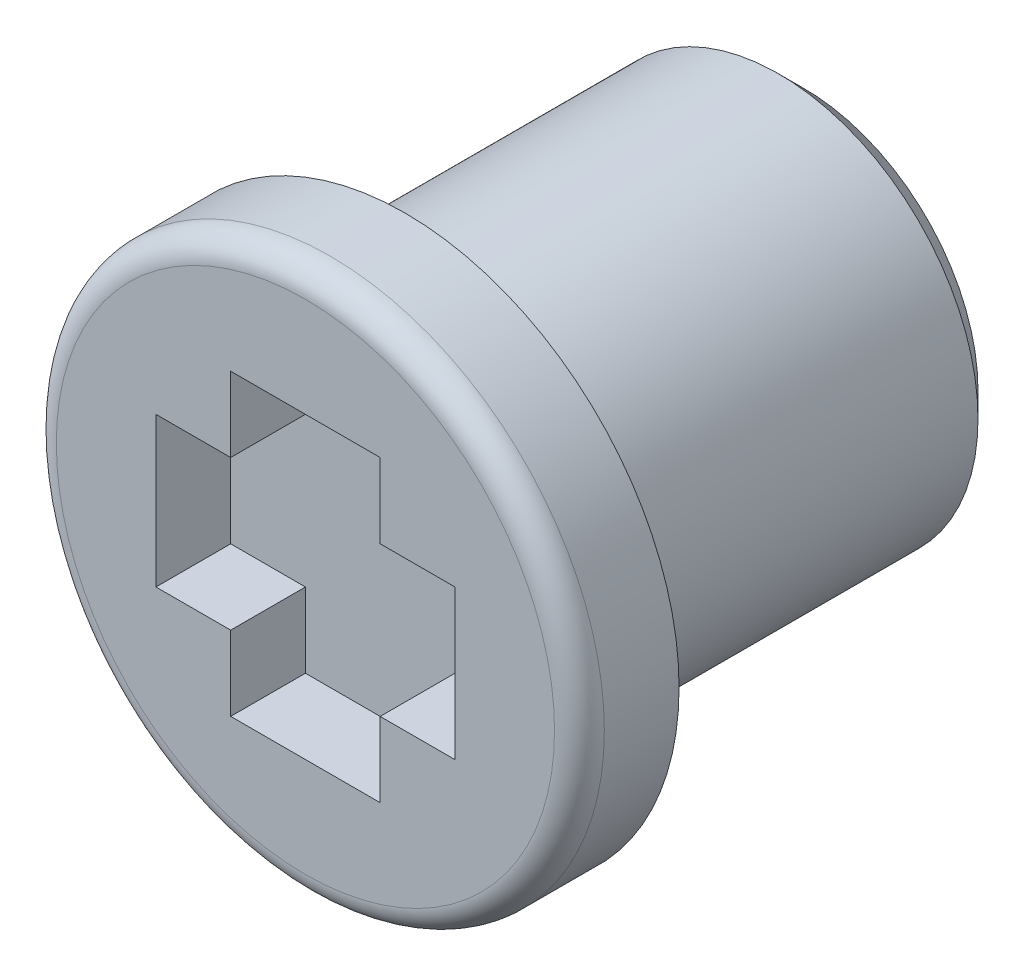
SolidWorks part; units mm, degrees
ref_plane "Front Plane" through (0, 0, 0) normal (0, 0, 1) x (1, 0, 0)
ref_plane "Top Plane" through (0, 0, 0) normal (0, 1, 0) x (1, 0, 0)
ref_plane "Right Plane" through (0, 0, 0) normal (1, 0, 0) x (0, 0, -1)
sketch "Sketch1" plane through (0, 0, 0) normal (0, 0, 1) x (1, 0, 0)
  circle A0 centre (0, 0.1694) radius 4
  dimension "D1" = 8
extrude "Boss-Extrude1" add sketch "Sketch1" along normal blind 8
sketch "Sketch2" plane through (0, 0, 8) normal (0, 0, 1) x (1, 0, 0)
  circle A0 centre (0, 0) radius 5.5
  dimension "D1" = 11
extrude "Boss-Extrude2" add sketch "Sketch2" along normal blind 2
chamfer "Chamfer1" distance 0.5 angle 45 1 edges at (4, 0.1694, 0)
sketch "Sketch4" plane through (0, 0, 10) normal (0, 0, 1) x (1, 0, 0)
  line L0 (-4.6717, 0) -> (-3, 0) construction
  line L2 (1.5, 1.5) -> (3, 1.5)
  line L3 (0, 3) -> (-1.5, 3)
  line L4 (-1.5, 3) -> (-1.5, 1.5)
  line L5 (-3, 0) -> (-3, 1.5)
  line L6 (-3, 1.5) -> (-1.5, 1.5)
  line L7 (0, 3) -> (1.5, 3)
  line L8 (1.5, 3) -> (1.5, 1.5)
  line L9 (-1.5, -3) -> (1.5, -3)
  line L10 (-3, 0) -> (-3, -1.5009)
  line L11 (-3, -1.5009) -> (-1.5, -1.5009)
  line L12 (3, 1.5) -> (3, -1.5009)
  line L13 (3, -1.5009) -> (1.5, -1.5009)
  line L14 (-1.5, -1.5009) -> (-1.5, -3)
  line L15 (1.5, -1.5009) -> (1.5, -3)
  line L16 (3, 0) -> (4.18, 0) construction
  dimension "D3" = 1.5
  dimension "D4" = 6
  dimension "D5" = 1.5
  dimension "D6" = 6
  dimension "D7" = 1.5
  dimension "D8" = 6
extrude "Cut-Extrude1" cut sketch "Sketch4" against normal blind 1.5
fillet "Fillet1" radius 0.5 1 edges at (5.5, 0, 10)
